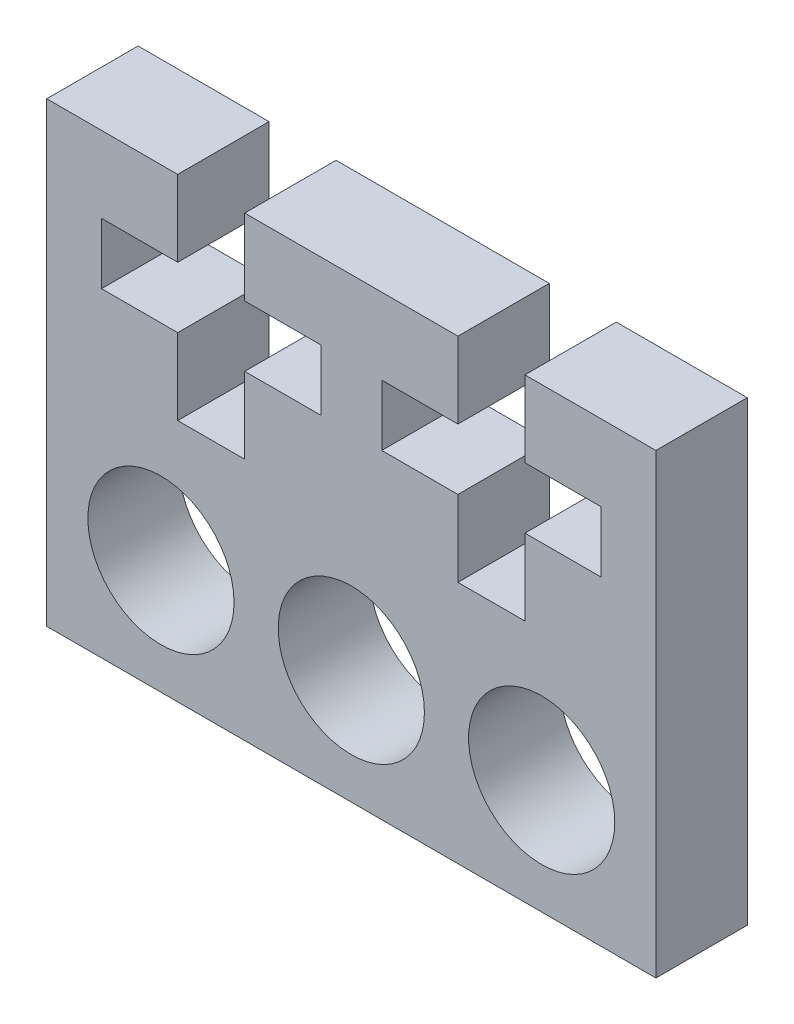
SolidWorks part; units mm, degrees
material "Acrylic (Medium-high impact)"
ref_plane "Front Plane" through (0, 0, 0) normal (0, 0, 1) x (1, 0, 0)
ref_plane "Top Plane" through (0, 0, 0) normal (0, 1, 0) x (1, 0, 0)
ref_plane "Right Plane" through (0, 0, 0) normal (1, 0, 0) x (0, 0, -1)
sketch "Sketch1" plane through (0, 0, 0) normal (0, 0, 1) x (1, 0, 0)
  line L0 (0, 7.5) -> (0, -7.5) construction
  line L1 (-10, -7.5) -> (10, -7.5)
  line L2 (-10, -7.5) -> (-10, 7.5)
  line L3 (-10, 7.5) -> (-5.7, 7.5)
  line L4 (10, -7.5) -> (10, 7.5)
  line L5 (-10, -7.5) -> (10, 7.5) construction
  line L6 (-10, 7.5) -> (10, -7.5) construction
  line L7 (-5.7, 7.5) -> (-5.7, 5)
  line L8 (-5.7, 5) -> (-8.2, 5)
  line L9 (-8.2, 5) -> (-8.2, 3)
  line L10 (-8.2, 3) -> (-5.7, 3)
  line L11 (-5.7, 3) -> (-5.7, 0.5)
  line L12 (-5.7, 0.5) -> (-3.5, 0.5)
  line L13 (-3.5, 0.5) -> (-3.5, 3)
  line L14 (-3.5, 3) -> (-1, 3)
  line L15 (-1, 3) -> (-1, 5)
  line L16 (-1, 5) -> (-3.5, 5)
  line L17 (-3.5, 5) -> (-3.5, 7.5)
  line L18 (3.5, 5) -> (3.5, 7.5)
  line L19 (1, 5) -> (3.5, 5)
  line L20 (1, 3) -> (1, 5)
  line L21 (3.5, 3) -> (1, 3)
  line L22 (3.5, 0.5) -> (3.5, 3)
  line L23 (5.7, 0.5) -> (3.5, 0.5)
  line L24 (5.7, 3) -> (5.7, 0.5)
  line L25 (8.2, 3) -> (5.7, 3)
  line L26 (8.2, 5) -> (8.2, 3)
  line L27 (5.7, 5) -> (8.2, 5)
  line L28 (5.7, 7.5) -> (5.7, 5)
  line L29 (-3.5, 7.5) -> (3.5, 7.5)
  line L30 (5.7, 7.5) -> (10, 7.5)
  circle A0 centre (0, -3.75) radius 2.4
  circle A1 centre (-6.25, -3.75) radius 2.4
  circle A2 centre (6.25, -3.75) radius 2.4
  point P0 (0, 0)
  dimension "D7" = 4.8
  dimension "D1" = 15
  dimension "D2" = 2.5
  dimension "D3" = 2
  dimension "D4" = 2.5
  dimension "D5" = 1.8
  dimension "D6" = 2.5
  dimension "D8" = 20
  dimension "D9" = 3.75
  dimension "D10" = 6.25
  dimension "D11" = 6.25
  dimension "D12" = 2.2
extrude "Boss-Extrude1" add sketch "Sketch1" along normal blind 3
